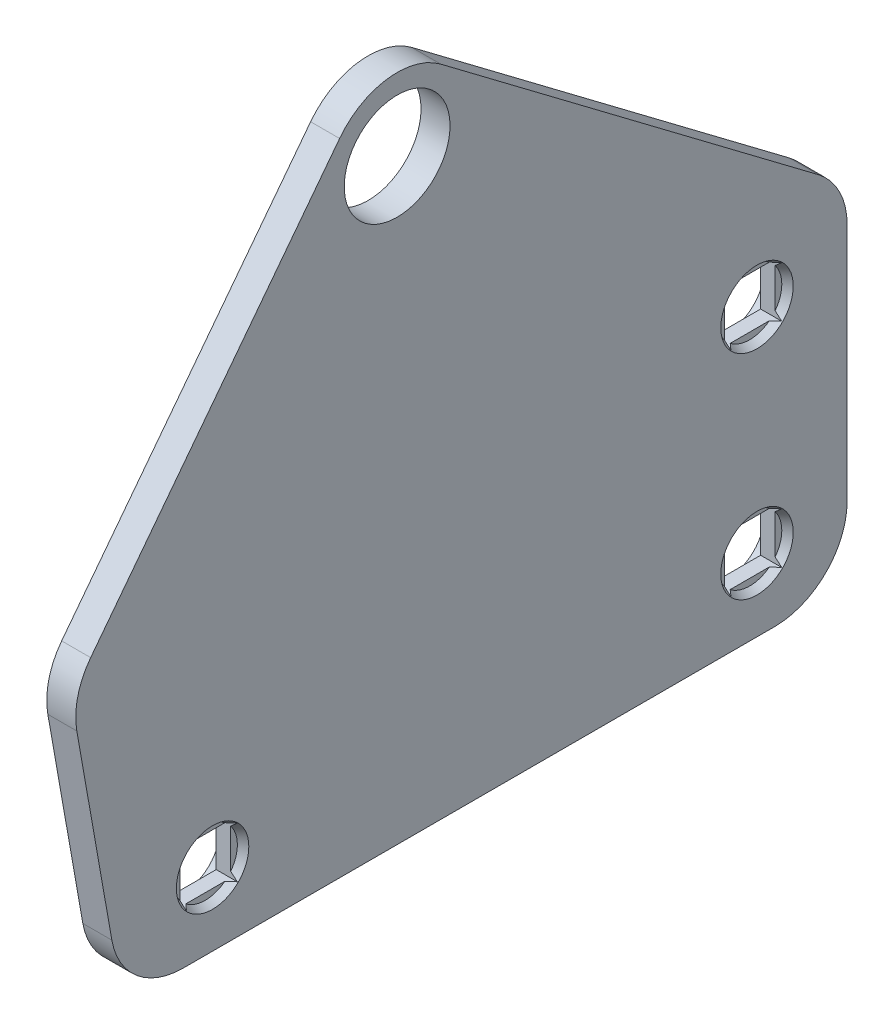
SolidWorks part; units mm, degrees
material "AISI 1020"
ref_plane "Front Plane" through (0, 0, 0) normal (0, 0, 1) x (1, 0, 0)
ref_plane "Top Plane" through (0, 0, 0) normal (0, 1, 0) x (1, 0, 0)
ref_plane "Right Plane" through (0, 0, 0) normal (1, 0, 0) x (0, 0, -1)
sketch "Sketch1" plane through (0, 0, 0) normal (1, 0, 0) x (0, 0, -1)
  line L0 (-20.4023, 0) -> (20.4023, 0)
  line L1 (-25.3263, 4.1318) -> (-27.7428, 17.8364)
  line L3 (-20.1277, 6.75) -> (-20.1277, 3.25)
  line L4 (-28.1243, 20) -> (-27.648, 20) construction
  line L5 (25.4023, 5) -> (25.4023, 21.5071)
  line L7 (25.4023, 24) -> (46.436, 24) construction
  line L9 (23.4113, 25.5003) -> (-2.6352, 45.1277)
  line L11 (-24.5977, 0) -> (-19.2077, 0) construction
  line L12 (-18.3777, 3.25) -> (-18.3777, 0) construction
  line L13 (0.4023, 0.9704) -> (0.4023, 25.9468) construction
  line L22 (20.9323, 6.75) -> (17.4323, 6.75)
  line L25 (17.4323, 21.4616) -> (20.9323, 21.4616)
  line L29 (-9.6142, 44.1743) -> (-26.7886, 21.7444)
  line L31 (-20.1277, 6.75) -> (-16.6277, 6.75)
  line L38 (-16.6277, 6.75) -> (-16.6277, 3.25)
  line L39 (-16.6277, 3.25) -> (-20.1277, 3.25)
  line L40 (17.4323, 6.75) -> (17.4323, 3.25)
  line L41 (17.4323, 3.25) -> (20.9323, 3.25)
  line L42 (20.9323, 3.25) -> (20.9323, 6.75)
  line L43 (17.4323, 21.4616) -> (17.4323, 17.9616)
  line L44 (20.9323, 21.4616) -> (20.9323, 17.9616)
  line L45 (20.9323, 17.9616) -> (17.4323, 17.9616)
  arc A5 (20.4023, 0) -> (25.4023, 5) centre (20.4023, 5) ccw
  arc A6 (-20.4023, 0) -> (-25.3263, 4.1318) centre (-20.4023, 5) cw
  arc A7 (25.4023, 21.5071) -> (23.4113, 25.5003) centre (20.4023, 21.5071) ccw
  arc A8 (-27.7428, 17.8364) -> (-26.7886, 21.7444) centre (-22.8187, 18.7046) cw
  arc A9 (-2.6352, 45.1277) -> (-9.6142, 44.1743) centre (-5.6443, 41.1346) ccw
  circle A10 centre (-5.6443, 41.1346) radius 3.65
  point P2 (0, 0)
  point P3 (19.1823, 21.4616)
  point P13 (17.4323, 5)
  point P15 (19.1823, 6.75)
  point P20 (-18.3777, 6.75)
  point P30 (-16.6277, 5)
  point P35 (25.4023, 0)
  dimension "D9" = 6.22
  dimension "D10" = 3.5
  dimension "D12" = 2.6352
  dimension "D6" = 7.3
  dimension "D13" = 5
  dimension "D1" = 50
  dimension "D2" = 100
  dimension "D3" = 20
  dimension "D4" = 143
  dimension "D5" = 24
  dimension "D7" = 3.5
  dimension "D8" = 6.22
  dimension "D11" = 3.5
  dimension "D14" = 3.5
  dimension "D15" = 5
  dimension "D16" = 3.5
  dimension "D17" = 6.22
  dimension "D18" = 14.7116
  dimension "D19" = 3.5
  dimension "D20" = 5
extrude "Boss-Extrude1" add sketch "Sketch1" along normal blind 2
sketch "Sketch3" plane through (2, 0, 0) normal (1, 0, 0) x (0, 0, -1)
  line L0 (-20.4023, 0) -> (20.4023, 0) construction
  line L1 (25.4023, 5) -> (25.4023, 21.5071) construction
  circle A0 centre (-18.3777, 5) radius 2.5
  circle A1 centre (19.1823, 5) radius 2.5
  circle A2 centre (19.1823, 19.712) radius 2.5
  dimension "D5" = 5
  dimension "D6" = 5
  dimension "D7" = 5
  dimension "D1" = 5
  dimension "D2" = 6.22
  dimension "D3" = 5
  dimension "D4" = 14.712
  dimension "D8" = 6.22
extrude "Cut-Extrude1" cut sketch "Sketch3" against normal blind 0.5 draft 30
sketch "Sketch5" plane through (0, 0, 0) normal (-1, 0, 0) x (0, 0, 1)
  line L0 (-25.4023, 5) -> (-25.4023, 21.5071) construction
  line L1 (20.4023, 0) -> (-20.4023, 0) construction
  circle A0 centre (-19.1823, 5) radius 2.5
  circle A1 centre (-19.1823, 19.7116) radius 2.5
  circle A2 centre (18.3777, 5) radius 2.5
  dimension "D1" = 5
  dimension "D2" = 5
  dimension "D3" = 5
  dimension "D4" = 6.22
  dimension "D5" = 14.7116
  dimension "D6" = 5
  dimension "D7" = 37.56
extrude "Cut-Extrude2" cut sketch "Sketch5" against normal blind 0.5
